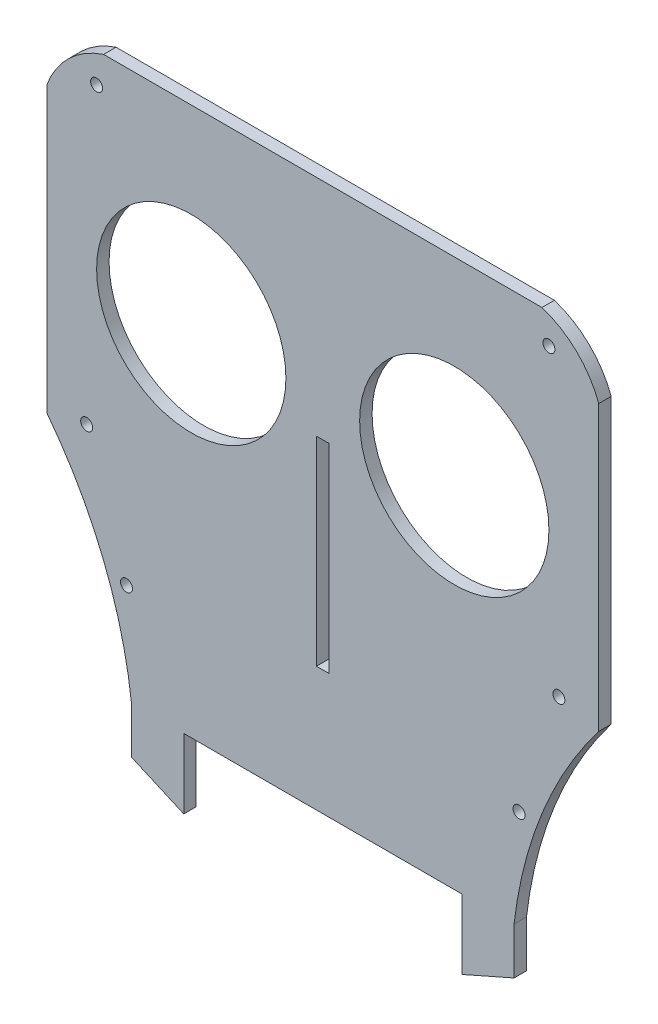
SolidWorks part; units mm, degrees
ref_plane "Front Plane" through (0, 0, 0) normal (0, 0, 1) x (1, 0, 0)
ref_plane "Top Plane" through (0, 0, 0) normal (0, 1, 0) x (1, 0, 0)
ref_plane "Right Plane" through (0, 0, 0) normal (1, 0, 0) x (0, 0, -1)
sketch "Sketch1" plane through (0, 0, 0) normal (0, 0, 1) x (1, 0, 0)
  line L0 (70.358, 0) -> (-70.358, 0)
  line L1 (-70.358, 0) -> (-70.358, -139.7)
  line L4 (-70.358, -139.7) -> (70.358, -139.7)
  line L5 (0, 0) -> (0, -139.7) construction
  line L8 (70.358, 0) -> (70.358, -139.7)
  dimension "D1" = 70.358
  dimension "D2" = 139.7
  dimension "D5" = 140.716
extrude "main body" add sketch "Sketch1" along normal blind 3.175
sketch "Sketch2" plane through (0, 0, 3.175) normal (0, 0, 1) x (1, 0, 0)
  line L0 (70.358, 0) -> (-70.358, 0) construction
  line L2 (-70.358, -139.7) -> (70.358, -139.7) construction
  line L3 (0, 0) -> (0, -139.7) construction
  circle A0 centre (-33.528, -48.26) radius 24.13
  point P71 (-52.324, -48.26)
  point P86 (-3.556, -48.26)
  point P87 (-3.556, -48.26)
  dimension "D3" = 33.528
  dimension "D6" = 48.26
  dimension "D2" = 48.26
extrude "cuts for eyes and motors" cut sketch "Sketch2" against normal through all
sketch "Sketch4" plane through (0, 0, 3.175) normal (0, 0, 1) x (1, 0, 0)
  line L0 (0, 0) -> (0, -139.7) construction
  line L1 (-70.358, -139.7) -> (70.358, -139.7) construction
  line L2 (0, -57.15) -> (0, -107.95) construction
  line L3 (-1.6129, -57.15) -> (1.6129, -57.15)
  line L4 (-1.6129, -57.15) -> (-1.6129, -107.95)
  line L5 (-1.6129, -107.95) -> (1.6129, -107.95)
  line L6 (1.6129, -57.15) -> (1.6129, -107.95)
  line L7 (70.358, 0) -> (-70.358, 0) construction
  dimension "D1" = 3.2258
  dimension "D2" = 50.8
  dimension "D3" = 57.15
extrude "cut for nose" cut sketch "Sketch4" against normal through all
mirror "Mirror1" about plane through (0, 0, 0) normal (1, 0, 0) of "cuts for eyes and motors"
sketch "Sketch11" plane through (0, 0, 3.175) normal (0, 0, 1) x (1, 0, 0)
  line L0 (-70.358, -139.7) -> (-70.358, -86.36)
  line L1 (-70.358, 0) -> (-70.358, -139.7) construction
  line L4 (-70.358, 0) -> (-70.358, -13.97)
  line L5 (-70.358, 0) -> (-55.88, 0)
  line L6 (70.358, 0) -> (-70.358, 0) construction
  line L8 (-70.358, -139.7) -> (70.358, -139.7) construction
  line L9 (-70.358, -139.7) -> (-48.768, -139.7)
  arc A0 (-70.358, -86.36) -> (-48.768, -139.7) centre (-156.0073, -152.067) cw
  arc A1 (-70.358, -13.97) -> (-55.88, 0) centre (-48.7264, -21.9009) cw
  dimension "D1" = 21.59
  dimension "D2" = 53.34
  dimension "D3" = 13.97
  dimension "D4" = 14.478
extrude "cut for rounded face features" cut sketch "Sketch11" against normal through all
mirror "mirror of rounded feature" about plane through (0, 0, 0) normal (1, 0, 0) of "cut for rounded face features"
sketch "Sketch12" plane through (0, 0, 3.175) normal (0, 0, 1) x (1, 0, 0)
  line L0 (-70.358, -13.97) -> (-70.358, -86.36) construction
  line L1 (55.88, 0) -> (-55.88, 0) construction
  circle A0 centre (-57.658, -7.62) radius 1.524
  circle A1 centre (-60.198, -83.82) radius 1.524
  circle A2 centre (-50.038, -114.3) radius 1.524
  dimension "D1" = 3.048
  dimension "D2" = 3.048
  dimension "D3" = 3.048
  dimension "D4" = 10.16
  dimension "D5" = 12.7
  dimension "D6" = 114.3
  dimension "D7" = 20.32
  dimension "D8" = 7.62
  dimension "D9" = 83.82
extrude "holes for spacers" cut sketch "Sketch12" against normal through all
mirror "mirror of spacer hole" about plane through (0, 0, 0) normal (1, 0, 0) of "holes for spacers"
sketch "Sketch14" plane through (0, 0, 3.175) normal (0, 0, 1) x (1, 0, 0)
  line L0 (-48.768, -139.7) -> (-35.433, -139.7)
  line L1 (-48.768, -139.7) -> (48.768, -139.7) construction
  line L2 (-35.433, -139.7) -> (-35.433, -157.48)
  line L3 (-35.433, -157.48) -> (-48.768, -151.5961)
  line L4 (-48.768, -151.5961) -> (-48.768, -139.7)
  dimension "D1" = 13.335
  dimension "D2" = 17.78
extrude "Boss-Extrude1" add sketch "Sketch14" against normal blind 3.175
mirror "Mirror3" about plane through (0, 0, 0) normal (1, 0, 0) of "Boss-Extrude1"
